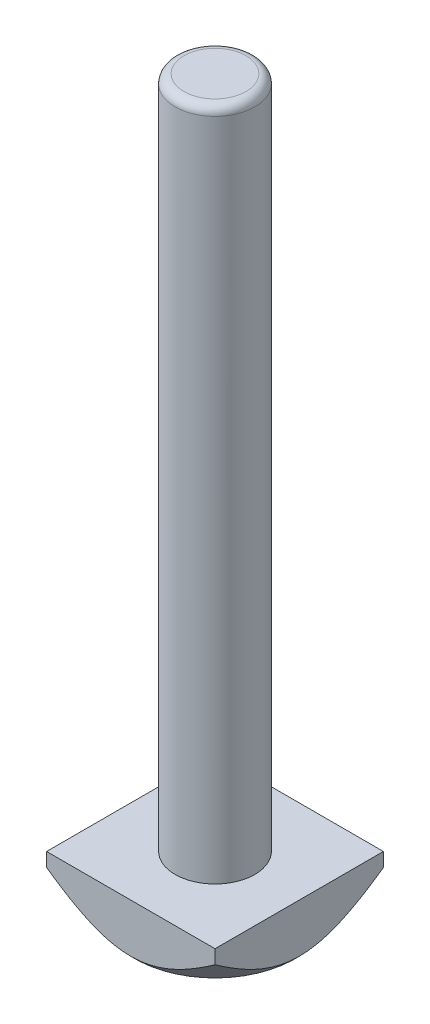
SolidWorks part; units mm, degrees
ref_plane "Front Plane" through (0, 0, 0) normal (0, 0, 1) x (1, 0, 0)
ref_plane "Top Plane" through (0, 0, 0) normal (0, 1, 0) x (1, 0, 0)
ref_plane "Right Plane" through (0, 0, 0) normal (1, 0, 0) x (0, 0, -1)
sketch "Sketch1" plane through (0, 0, 0) normal (0, 1, 0) x (1, 0, 0)
  line L1 (-9.5, -9.5) -> (9.5, -9.5)
  line L2 (-9.5, -9.5) -> (-9.5, 9.5)
  line L3 (-9.5, 9.5) -> (9.5, 9.5)
  line L4 (9.5, -9.5) -> (9.5, 9.5)
  line L5 (-9.5, -9.5) -> (9.5, 9.5) construction
  line L6 (-9.5, 9.5) -> (9.5, -9.5) construction
  point P0 (0, 0)
  dimension "D1" = 19
  dimension "D2" = 19
extrude "Boss-Extrude1" add sketch "Sketch1" along normal blind 6
sketch "Sketch2" plane through (0, 6, 0) normal (0, 1, 0) x (1, 0, 0)
  circle A0 centre (0, 0) radius 4.5
  dimension "D1" = 4.5
extrude "Boss-Extrude2" add sketch "Sketch2" along normal blind 76
sketch "Sketch3" plane through (0, 0, 0) normal (0, -1, 0) x (1, 0, 0)
  circle A0 centre (0, 0) radius 9
  dimension "D1" = 9
extrude "Cut-Extrude1" cut sketch "Sketch3" against normal blind 76 draft 45 flip side to cut
fillet "Fillet1" radius 1 1 edges at (0, 82, 4.5)
